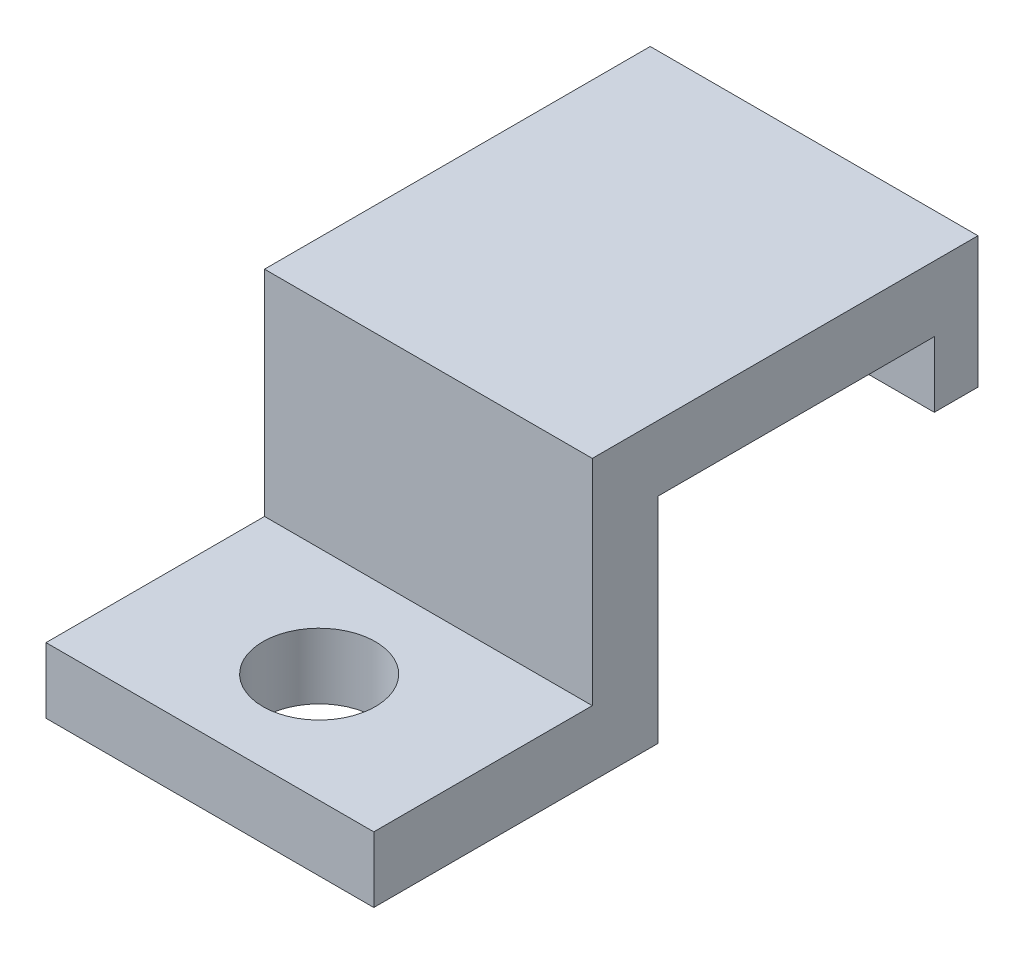
SolidWorks part; units mm, degrees
ref_plane "Alzado" through (0, 0, 0) normal (0, 0, 1) x (1, 0, 0)
ref_plane "Planta" through (0, 0, 0) normal (0, 1, 0) x (1, 0, 0)
ref_plane "Vista lateral" through (0, 0, 0) normal (1, 0, 0) x (0, 0, -1)
sketch "Croquis2" plane through (0, 0, 0) normal (1, 0, 0) x (0, 0, -1)
  line L0 (0, 0) -> (13, 0)
  line L1 (13, 0) -> (13, 9.8)
  line L2 (13, 9.8) -> (25.65, 9.8)
  line L3 (25.65, 9.8) -> (25.65, 12.8)
  line L4 (25.65, 12.8) -> (10, 12.8)
  line L5 (10, 12.8) -> (10, 3)
  line L6 (10, 3) -> (0, 3)
  line L7 (0, 3) -> (0, 0)
  dimension "D1" = 12.65
  dimension "D2" = 3
  dimension "D3" = 3
  dimension "D4" = 3
  dimension "D5" = 10
  dimension "D6" = 9.8
extrude "Saliente-Extruir1" add sketch "Croquis2" along normal blind 15
sketch "Croquis4" plane through (0, 0, 0) normal (1, 0, 0) x (0, 0, -1)
  line L0 (13, 9.8) -> (25.65, 9.8) construction
  line L1 (25.65, 12.8) -> (27.65, 12.8)
  line L2 (25.65, 12.8) -> (25.65, 6.8)
  line L3 (25.65, 6.8) -> (27.65, 6.8)
  line L4 (27.65, 12.8) -> (27.65, 6.8)
  dimension "D1" = 2
  dimension "D2" = 3
extrude "Saliente-Extruir2" add sketch "Croquis4" along normal through all
sketch "Croquis5" plane through (0, 3, 0) normal (0, 1, 0) x (1, 0, 0)
  line L0 (0, 0) -> (15, 10) construction
  circle A0 centre (7.5, 5) radius 2.575
  dimension "D1" = 5.15
extrude "Cortar-Extruir1" cut sketch "Croquis5" against normal through all
